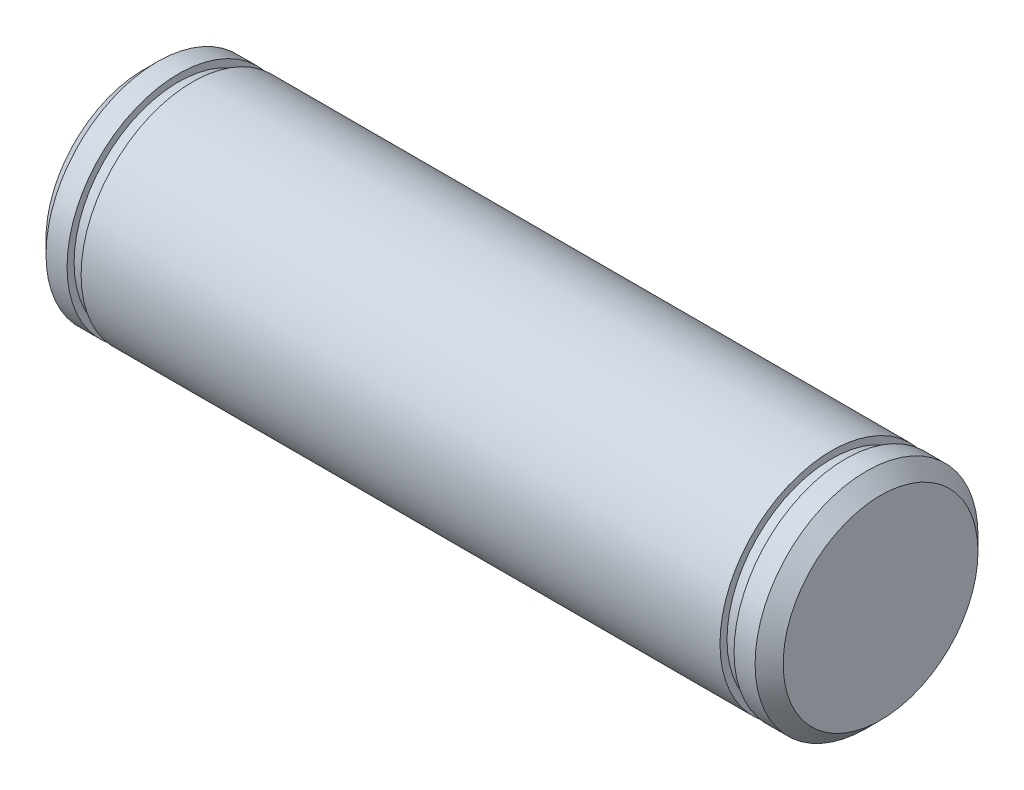
SolidWorks part; units mm, degrees
ref_plane "Front Plane" through (0, 0, 0) normal (0, 0, 1) x (1, 0, 0)
ref_plane "Top Plane" through (0, 0, 0) normal (0, 1, 0) x (1, 0, 0)
ref_plane "Right Plane" through (0, 0, 0) normal (1, 0, 0) x (0, 0, -1)
sketch "Sketch1" plane through (0, 0, 0) normal (1, 0, 0) x (0, 0, -1)
  circle A0 centre (0, 0) radius 15.875
  dimension "D1" = 31.75
extrude "Boss-Extrude1" add sketch "Sketch1" along normal mid plane 105
chamfer "Chamfer1" distance 2 angle 45 2 edges at (-52.5, 0, -15.875) (52.5, 0, -15.875)
ref_plane "Plane1" through (-47.5, 0, 0) normal (-1, 0, 0) x (0, 0, 1)
sketch "Sketch2" plane through (-47.5, 0, 0) normal (-1, 0, 0) x (0, 0, 1)
  circle A0 centre (0, 0) radius 15.875
  circle A1 centre (0, 0) radius 14.875
  dimension "D1" = 29.75
  dimension "D2" = 31.75
extrude "Cut-Extrude1" cut sketch "Sketch2" against normal blind 2
mirror "Mirror1" about plane through (0, 0, 0) normal (1, 0, 0) of "Cut-Extrude1"
